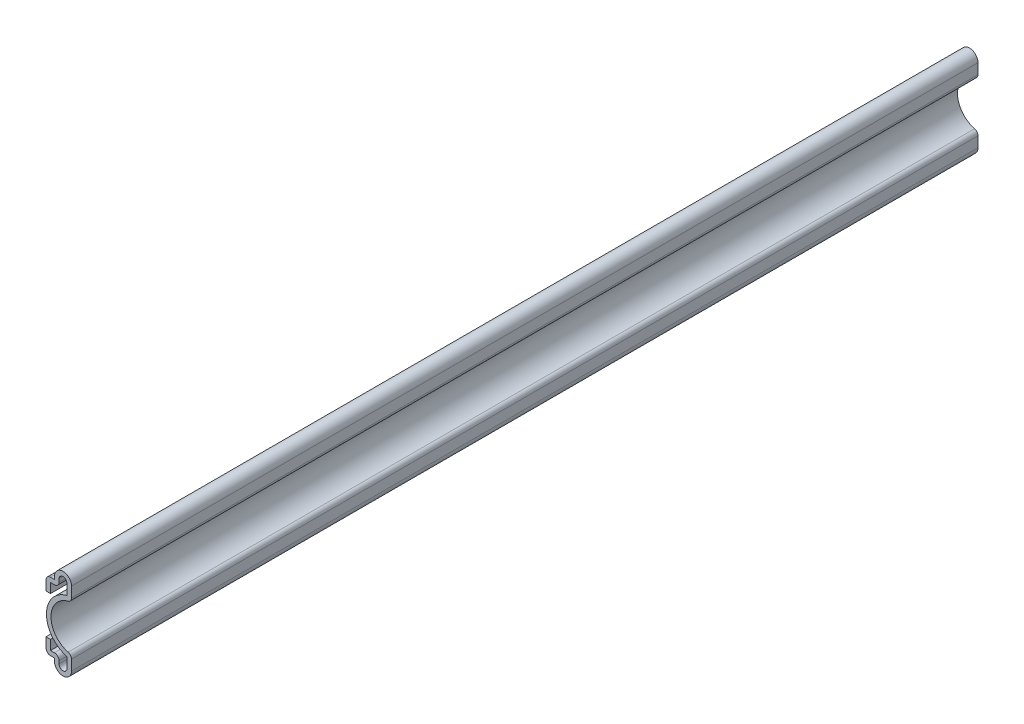
SolidWorks part; units mm, degrees
ref_plane "Front Plane" through (0, 0, 0) normal (0, 0, 1) x (1, 0, 0)
ref_plane "Top Plane" through (0, 0, 0) normal (0, 1, 0) x (1, 0, 0)
ref_plane "Right Plane" through (0, 0, 0) normal (1, 0, 0) x (0, 0, -1)
sketch "Sketch1" plane through (0, 0, 0) normal (0, 0, 1) x (1, 0, 0)
  line L0 (-7.1438, 0) -> (0, 0) construction
  line L1 (0, 0) -> (0, 29.1158) construction
  line L2 (-7.1438, 7.1438) -> (-7.1438, 3.175)
  line L3 (-7.1438, 3.175) -> (-4.7625, 3.175)
  line L4 (-4.7625, 3.175) -> (-4.7625, 2.3812)
  line L5 (0, 2.3813) -> (0, 6.35)
  line L6 (0.6349, 12.7) -> (10.9802, 12.7) construction
  line L7 (0, 23.0187) -> (0, 19.05)
  line L8 (-4.7625, 22.225) -> (-4.7625, 23.0188)
  line L9 (-7.1438, 22.225) -> (-4.7625, 22.225)
  line L10 (-7.1438, 18.2562) -> (-7.1438, 22.225)
  arc A0 (-4.7625, 2.3812) -> (0, 2.3813) centre (-2.3812, 2.3813) ccw
  arc A1 (0, 6.35) -> (0, 19.05) centre (0.6349, 12.7) cw
  arc A2 (-4.7625, 23.0188) -> (0, 23.0187) centre (-2.3813, 23.0187) cw
  point P20 (-4.7625, 18.2466)
  point P21 (0, 29.1158)
  dimension "D2" = 2.3813
  dimension "D7" = 1.397
  dimension "D8" = 25.4
  dimension "D1" = 6.35
  dimension "D3" = 2.3813
  dimension "D4" = 7.1438
  dimension "D5" = 3.9688
  dimension "D6" = 3.175
extrude "Extrude-Thin1" add sketch "Sketch1" against normal blind 254 thin thin type one direction wall 1.27
fillet "Fillet1" radius 1.27 6 edges at (0, 19.05, -127) (0, 6.35, -127) (-7.1438, 3.175, -127) (-3.4925, 4.445, -127) (-3.4925, 20.955, -127) (-7.1438, 22.225, -127)
